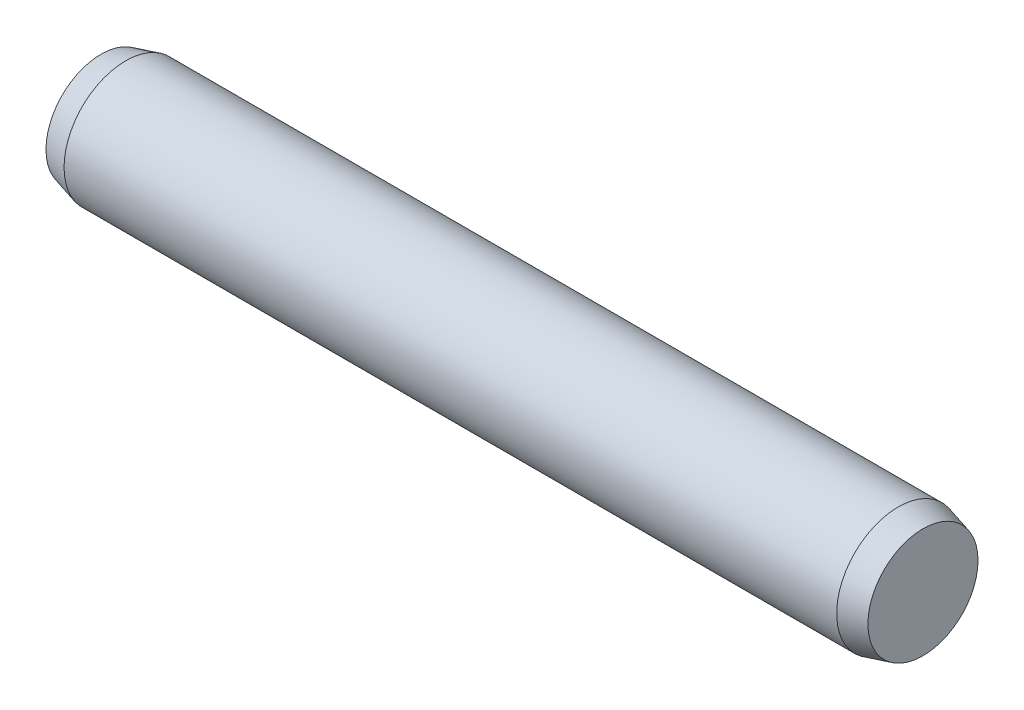
SolidWorks part; units mm, degrees
ref_plane "Front Plane" through (0, 0, 0) normal (0, 0, 1) x (1, 0, 0)
ref_plane "Top Plane" through (0, 0, 0) normal (0, 1, 0) x (1, 0, 0)
ref_plane "Right Plane" through (0, 0, 0) normal (1, 0, 0) x (0, 0, -1)
sketch "Sketch1" plane through (0, 0, 0) normal (0, 0, 1) x (1, 0, 0)
  line L0 (-18.8, 0) -> (18.8, 0) construction
  line L1 (18.8, 3) -> (18.8, -3) construction
  line L2 (-18.8, 3) -> (-18.8, -3) construction
  line L3 (20, 3) -> (20, -3) construction
  line L4 (-20, 3) -> (-20, -3) construction
  line L5 (-18.8, 0) -> (-20, 0) construction
  line L6 (18.8, 0) -> (20, 0) construction
  dimension "Dia" = 6
  dimension "C" = 1.2
  dimension "D1" = 1.2
  dimension "Length" = 40
sketch "Sketch2" plane through (0, 0, 0) normal (1, 0, 0) x (0, 0, -1)
  circle A0 centre (0, 0) radius 3
extrude "Extrude1" add sketch "Sketch2" against normal up to vertex (18.8 mm away) and the other way up to vertex (18.8 mm away) up to point (-18.8, 3, 0) other way up to point (18.8, 3, 0)
sketch "Sketch3" plane through (18.8, 0, 0) normal (1, 0, 0) x (0, 0, -1)
  circle A1 centre (0, 0) radius 3
  circle A2 centre (0, 0) radius 3
  dimension "D1" = 0
extrude "Extrude2" add sketch "Sketch3" along normal up to vertex (1.2 mm away) draft 15 up to point (20, 0, 0)
sketch "Sketch4" plane through (-18.8, 0, 0) normal (-1, 0, 0) x (0, 0, 1)
  circle A1 centre (0, 0) radius 3
  circle A2 centre (0, 0) radius 3
  dimension "D1" = 0
extrude "Extrude3" add sketch "Sketch4" along normal up to vertex (1.2 mm away) draft 15 up to point (-20, 0, 0)
equation "\"D1@Sketch1\" = \"C@Sketch1\""
